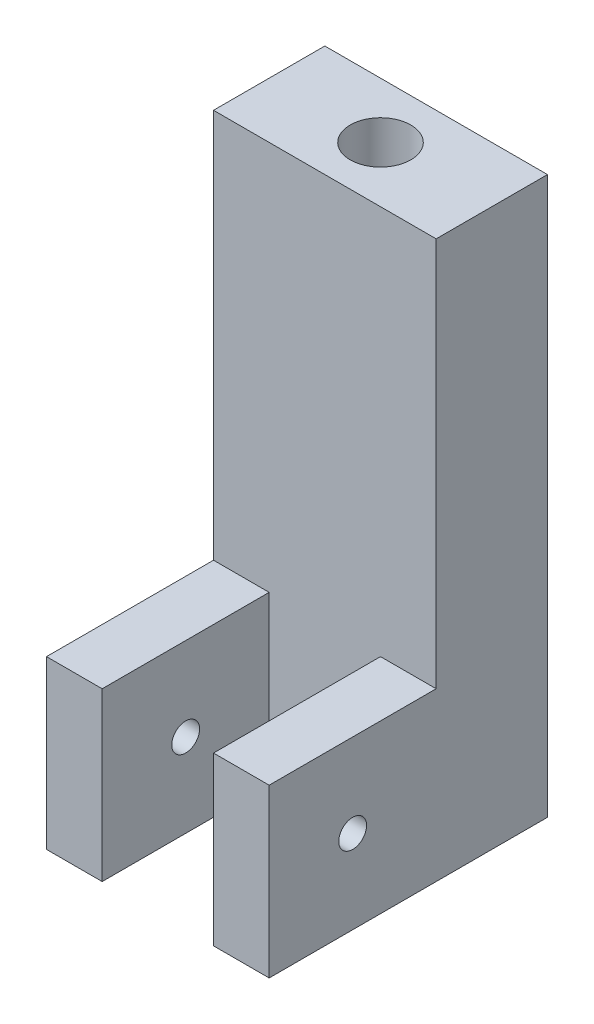
SolidWorks part; units mm, degrees
material "6061-T6 (SS)"
ref_plane "Front Plane" through (0, 0, 0) normal (0, 0, 1) x (1, 0, 0)
ref_plane "Top Plane" through (0, 0, 0) normal (0, 1, 0) x (1, 0, 0)
ref_plane "Right Plane" through (0, 0, 0) normal (1, 0, 0) x (0, 0, -1)
sketch "Sketch1" plane through (0, 0, 0) normal (1, 0, 0) x (0, 0, -1)
  line L2 (0, 0) -> (0, 63.5)
  line L3 (0, 63.5) -> (-12.7, 63.5)
  line L4 (-12.7, 19.05) -> (-12.7, 63.5)
  line L5 (0, 0) -> (-31.75, 0)
  line L7 (-12.7, 19.05) -> (-31.75, 19.05)
  line L8 (-31.75, 0) -> (-31.75, 19.05)
  dimension "D1" = 63.5
  dimension "D2" = 19.05
  dimension "D3" = 12.7
  dimension "D4" = 31.75
extrude "Boss-Extrude1" add sketch "Sketch1" along normal blind 25.4
sketch "Sketch2" plane through (25.4, 0, 0) normal (1, 0, 0) x (0, 0, -1)
  line L0 (-31.75, 19.05) -> (-31.75, 0) construction
  line L1 (-12.7, 19.05) -> (-31.75, 19.05) construction
  circle A0 centre (-22.225, 9.525) radius 1.5875
  dimension "D3" = 3.175
  dimension "D1" = 9.525
  dimension "D2" = 9.525
extrude "Cut-Extrude1" cut sketch "Sketch2" against normal through all
sketch "Sketch3" plane through (0, 0, 31.75) normal (0, 0, 1) x (1, 0, 0)
  line L0 (25.4, 0) -> (0, 0) construction
  line L1 (6.35, 0) -> (19.05, 0)
  line L2 (6.35, 0) -> (6.35, 19.05)
  line L3 (6.35, 19.05) -> (19.05, 19.05)
  line L4 (19.05, 0) -> (19.05, 19.05)
  line L5 (25.4, 19.05) -> (0, 19.05) construction
  line L6 (0, 19.05) -> (0, 0) construction
  dimension "D1" = 12.7
  dimension "D2" = 6.35
extrude "Cut-Extrude2" cut sketch "Sketch3" against normal blind 19.05
hole_wizard "5/16-24 Tapped Hole1" positions "Sketch4" profile "Sketch5" tap size "5/16-24" standard "ANSI Inch" end condition through all
sketch "Sketch4" plane through (0, 63.5, 0) normal (0, 1, 0) x (1, 0, 0)
  line L0 (0, -6.35) -> (25.4, -6.35) construction
  line L1 (0, 0) -> (0, -12.7) construction
  line L2 (25.4, 0) -> (25.4, -12.7) construction
  point P0 (12.7, -6.35)
cosmetic thread "Hole Thread1" parameters "D1"=25.4, "D2"=7.9375
sketch "Sketch5" plane through (12.7, 63.5, 6.35) normal (1, 0, 0) x (0, 0, 1)
  line L0 (0, 0) -> (0, 63.5)
  line L1 (0, 63.5) -> (3.4544, 63.5)
  line L2 (3.4544, 63.5) -> (3.4544, 0)
  line L5 (3.4544, 0) -> (0, 0)
  line L11 (0, -6.35) -> (0, 107.95) construction
  dimension "Thru Tap Drill Dia." = 6.9088
  dimension "Thru Tap Drill Depth" = 63.5
